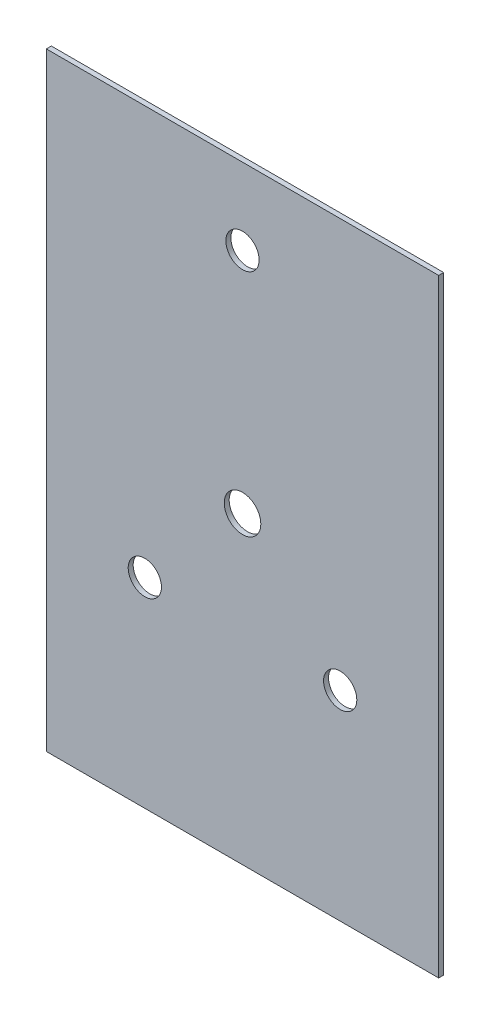
SolidWorks part; units mm, degrees
ref_plane "Alzado" through (0, 0, 0) normal (0, 0, 1) x (1, 0, 0)
ref_plane "Planta" through (0, 0, 0) normal (0, 1, 0) x (1, 0, 0)
ref_plane "Vista lateral" through (0, 0, 0) normal (1, 0, 0) x (0, 0, -1)
sketch "Sketch1" plane through (0, 0, 0) normal (0, 0, 1) x (1, 0, 0)
  line L1 (-118, 183) -> (118, 183)
  line L2 (-118, 183) -> (-118, -183)
  line L3 (-118, -183) -> (118, -183)
  line L4 (118, 183) -> (118, -183)
  line L5 (-118, 183) -> (118, -183) construction
  line L6 (-118, -183) -> (118, 183) construction
  point P0 (0, 0)
  dimension "D1" = 236
  dimension "D2" = 366
extrude "Boss-Extrude1" add sketch "Sketch1" along normal blind 3
sketch "Sketch2" plane through (0, 0, 0) normal (0, 0, -1) x (-1, 0, 0)
  circle A1 centre (0, 137.5) radius 7.5
  dimension "D1" = 15
extrude "Cut-Extrude2" cut sketch "Sketch2" against normal up to next
sketch "Sketch3" plane through (0, 0, 3) normal (0, 0, 1) x (1, 0, 0)
  circle A0 centre (0, 0) radius 11
  circle A1 centre (-58.75, -62.75) radius 10
  circle A2 centre (58.75, -62.75) radius 10
  circle A3 centre (0, 137.0156) radius 10
  dimension "D1" = 20
  dimension "D2" = 22
extrude "Cut-Extrude3" cut sketch "Sketch3" against normal up to next
sketch "Sketch4" plane through (0, 0, 0) normal (0, 0, 1) x (1, 0, 0)
  circle A0 centre (0, 0) radius 11
  circle A3 centre (0, 137.0156) radius 9
  dimension "D2" = 22
extrude "Cut-Extrude5" [suppressed] cut sketch "Sketch4" along normal up to next contours A0
